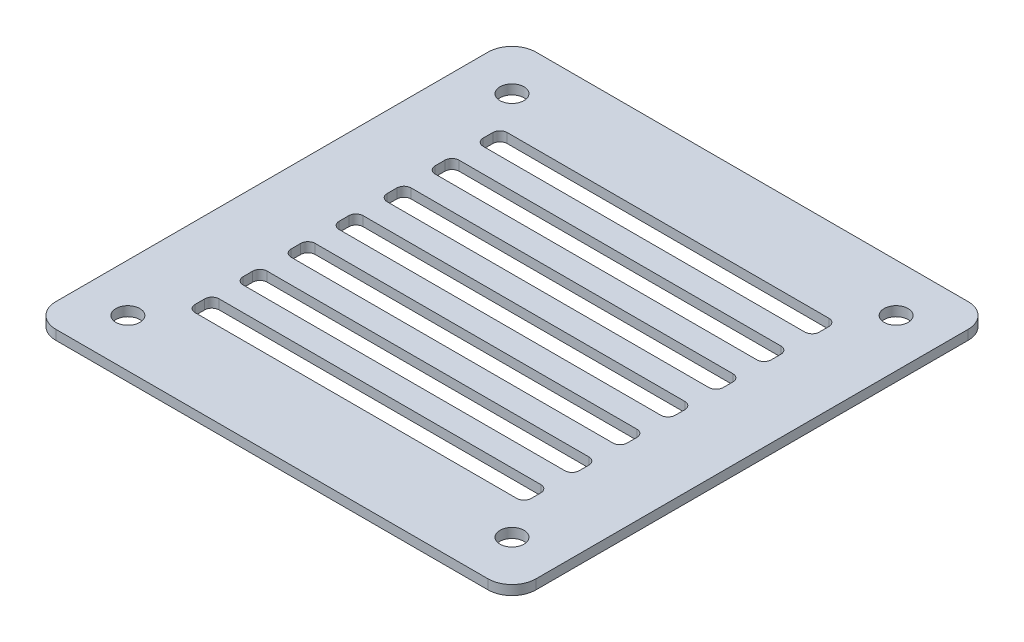
SolidWorks part; units mm, degrees
ref_plane "Front Plane" through (0, 0, 0) normal (0, 0, 1) x (1, 0, 0)
ref_plane "Top Plane" through (0, 0, 0) normal (0, 1, 0) x (1, 0, 0)
ref_plane "Right Plane" through (0, 0, 0) normal (1, 0, 0) x (0, 0, -1)
sketch "Sketch1" plane through (0, 0, 0) normal (0, 1, 0) x (1, 0, 0)
  line L0 (0, 0) -> (0, -32.5) construction
  line L1 (-50, 50) -> (50, 50)
  line L2 (-50, 50) -> (-50, -50)
  line L3 (-50, -50) -> (50, -50)
  line L4 (50, 50) -> (50, -50)
  line L5 (-50, 50) -> (50, -50) construction
  line L6 (-50, -50) -> (50, 50) construction
  line L7 (-35, -32.5) -> (35, -32.5)
  line L8 (-35, -32.5) -> (-35, -27.5)
  line L9 (-35, -27.5) -> (35, -27.5)
  line L10 (35, -32.5) -> (35, -27.5)
  line L11 (-35, -32.5) -> (35, -27.5) construction
  line L12 (-35, -27.5) -> (35, -32.5) construction
  line L13 (-35, -22.5) -> (35, -22.5)
  line L14 (-35, -22.5) -> (-35, -17.5)
  line L15 (-35, -17.5) -> (35, -17.5)
  line L16 (35, -22.5) -> (35, -17.5)
  line L17 (-35, -12.5) -> (35, -12.5)
  line L18 (-35, -12.5) -> (-35, -7.5)
  line L19 (-35, -7.5) -> (35, -7.5)
  line L20 (35, -12.5) -> (35, -7.5)
  line L21 (-35, -2.5) -> (35, -2.5)
  line L22 (-35, -2.5) -> (-35, 2.5)
  line L23 (-35, 2.5) -> (35, 2.5)
  line L24 (35, -2.5) -> (35, 2.5)
  line L25 (-35, 7.5) -> (35, 7.5)
  line L26 (-35, 7.5) -> (-35, 12.5)
  line L27 (-35, 12.5) -> (35, 12.5)
  line L28 (35, 7.5) -> (35, 12.5)
  line L29 (-35, 17.5) -> (35, 17.5)
  line L30 (-35, 17.5) -> (-35, 22.5)
  line L31 (-35, 22.5) -> (35, 22.5)
  line L32 (35, 17.5) -> (35, 22.5)
  line L33 (-35, 27.5) -> (35, 27.5)
  line L34 (-35, 27.5) -> (-35, 32.5)
  line L35 (-35, 32.5) -> (35, 32.5)
  line L36 (35, 27.5) -> (35, 32.5)
  line L37 (-35, 0) -> (35, 0) construction
  circle A1 centre (-40, 40) radius 2.5
  circle A4 centre (40, 40) radius 2.5
  circle A5 centre (40, -40) radius 2.5
  circle A6 centre (-40, -40) radius 2.5
  point P0 (0, 0)
  point P5 (0, -30)
  point P19 (0, 0)
  dimension "D1" = 5
  dimension "D4" = 5
  dimension "D5" = 10
  dimension "D6" = 4
  dimension "D2" = 100
  dimension "D3" = 100
  dimension "D7" = 70
  dimension "D9" = 10
  dimension "D8" = 7
extrude "Boss-Extrude1" add sketch "Sketch1" along normal blind 2
fillet "Fillet1" radius 5 4 edges at (50, 1, 50) (-50, 1, -50) (50, 1, -50) (-50, 1, 50)
fillet "Fillet2" radius 1.5 28 edges at (-35, 1, -32.5) (35, 1, -27.5) (35, 1, -32.5) (-35, 1, -27.5) (-35, 1, -22.5) (35, 1, -17.5) (35, 1, -22.5) (-35, 1, -17.5) (-35, 1, -12.5) (35, 1, -7.5) (35, 1, -12.5) (-35, 1, -7.5) (-35, 1, -2.5) (35, 1, 2.5) (35, 1, -2.5) (-35, 1, 2.5) (-35, 1, 7.5) (35, 1, 12.5) (35, 1, 7.5) (-35, 1, 12.5) (-35, 1, 17.5) (35, 1, 22.5) (35, 1, 17.5) (-35, 1, 22.5) (-35, 1, 27.5) (35, 1, 32.5) (35, 1, 27.5) (-35, 1, 32.5)
